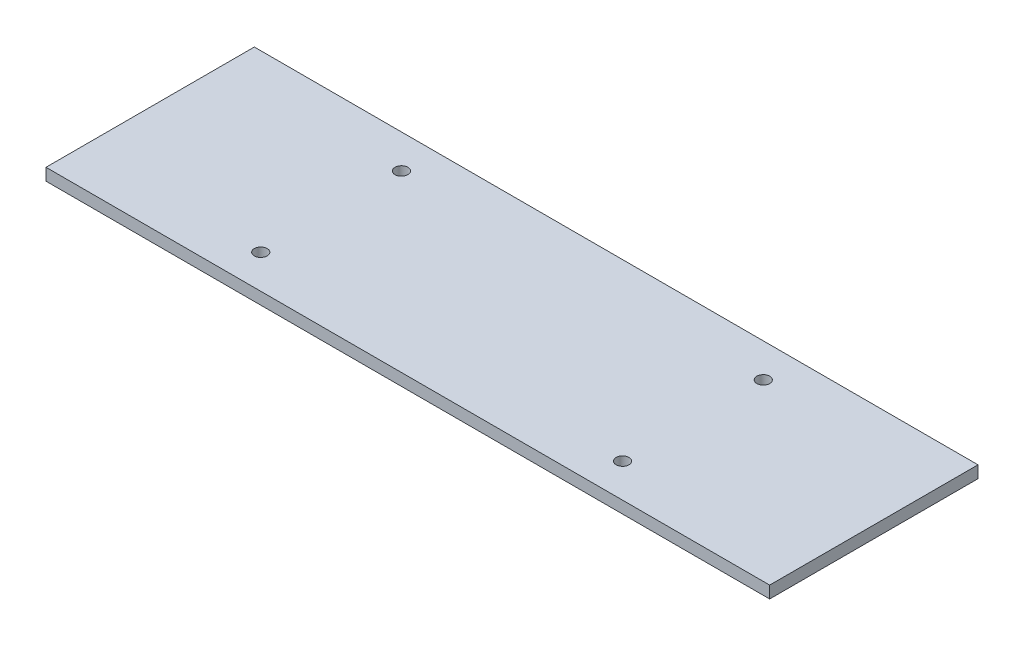
SolidWorks part; units mm, degrees
ref_plane "Front Plane" through (0, 0, 0) normal (0, 0, 1) x (1, 0, 0)
ref_plane "Top Plane" through (0, 0, 0) normal (0, 1, 0) x (1, 0, 0)
ref_plane "Right Plane" through (0, 0, 0) normal (1, 0, 0) x (0, 0, -1)
sketch "Sketch1" plane through (0, 0, 0) normal (0, 1, 0) x (1, 0, 0)
  line L1 (-63.4078, 26.6263) -> (116.5922, 26.6263)
  line L2 (-63.4078, 26.6263) -> (-63.4078, -25.1937)
  line L3 (-63.4078, -25.1937) -> (116.5922, -25.1937)
  line L4 (116.5922, 26.6263) -> (116.5922, -25.1937)
  dimension "D1" = 51.82
  dimension "D2" = 180
extrude "Boss-Extrude1" add sketch "Sketch1" along normal blind 3
sketch "Sketch2" plane through (0, 3, 0) normal (0, 1, 0) x (1, 0, 0)
  line L0 (-63.4078, 26.6263) -> (116.5922, 26.6263) construction
  line L1 (-63.4078, 26.6263) -> (-63.4078, -25.1937) construction
  circle A0 centre (-18.4078, 18.2163) radius 1.6
  circle A1 centre (71.5922, 18.2163) radius 1.6
  circle A2 centre (71.5922, -16.7837) radius 1.6
  circle A3 centre (-18.4078, -16.7837) radius 1.6
  dimension "D1" = 3.2
  dimension "D2" = 3.2
  dimension "D3" = 3.2
  dimension "D4" = 3.2
  dimension "D5" = 90
  dimension "D6" = 90
  dimension "D7" = 35
  dimension "D8" = 35
  dimension "D9" = 8.41
  dimension "D10" = 8.41
  dimension "D11" = 45
extrude "HoodBoard" cut sketch "Sketch2" against normal through all
